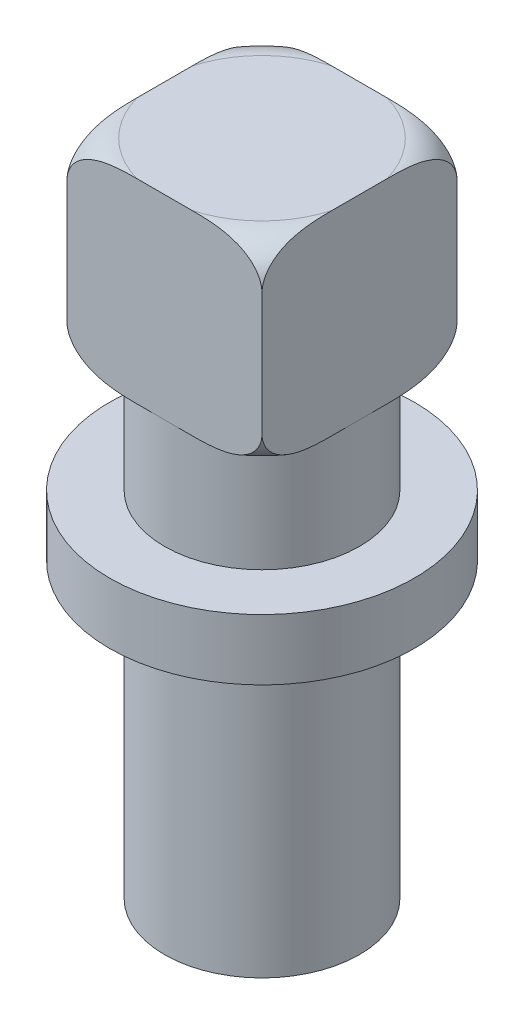
SolidWorks part; units mm, degrees
ref_plane "Front Plane" through (0, 0, 0) normal (0, 0, 1) x (1, 0, 0)
ref_plane "Top Plane" through (0, 0, 0) normal (0, 1, 0) x (1, 0, 0)
ref_plane "Right Plane" through (0, 0, 0) normal (1, 0, 0) x (0, 0, -1)
sketch "Sketch1" plane through (0, 0, 0) normal (0, 0, 1) x (1, 0, 0)
  line L0 (0, 0) -> (8, 0)
  line L1 (8, 0) -> (8, 24)
  line L2 (8, 24) -> (12.5, 24)
  line L3 (12.5, 24) -> (12.5, 29)
  line L4 (12.5, 29) -> (8, 29)
  line L5 (8, 29) -> (8, 38)
  line L6 (8, 38) -> (0, 38)
  line L7 (0, 0) -> (0, 44.1574) construction
  line L8 (0, 0) -> (0, 38)
  dimension "D1" = 8
  dimension "D2" = 24
  dimension "D3" = 5
  dimension "D4" = 9
  dimension "D5" = 12.5
revolve "Revolve1" add sketch "Sketch1" angle 360 about L7
sketch "Sketch2" plane through (0, 38, 0) normal (0, 1, 0) x (1, 0, 0)
  line L1 (-8, 8) -> (8, 8)
  line L2 (-8, 8) -> (-8, -8)
  line L3 (-8, -8) -> (8, -8)
  line L4 (8, 8) -> (8, -8)
  line L5 (0, -8) -> (0, 8) construction
  line L6 (-8, 0) -> (8, 0) construction
  point P0 (0, 0)
  dimension "D1" = 16
  dimension "D2" = 16
extrude "Boss-Extrude1" add sketch "Sketch2" along normal blind 16
ref_plane "Plane1" through (0, 0, 0) normal (0.7071, 0, 0.7071) x (0.7071, 0, -0.7071)
sketch "Sketch3" plane through (0, 0, 0) normal (0.7071, 0, 0.7071) x (0.7071, 0, -0.7071)
  line L0 (11.3137, 54) -> (8.3137, 54)
  line L1 (0, 54) -> (11.3137, 54) construction
  line L2 (11.3137, 51) -> (11.3137, 54)
  line L3 (11.3137, 54) -> (11.3137, 38) construction
  line L4 (11.3137, 38) -> (8.3137, 38)
  line L5 (-5.6569, 38) -> (5.6569, 38) construction
  line L6 (11.3137, 41) -> (11.3137, 38)
  line L7 (0, 34.9711) -> (0, -34.9711) construction
  line L8 (0, 54) -> (0, 38) construction
  arc A0 (8.3137, 54) -> (11.3137, 51) centre (8.3137, 51) cw
  arc A1 (11.3137, 41) -> (8.3137, 38) centre (8.3137, 41) cw
  point P16 (11.3137, 54)
  point P19 (11.3137, 38)
  dimension "D1" = 3
revolve "Cut-Revolve1" cut sketch "Sketch3" angle 360 about L7
